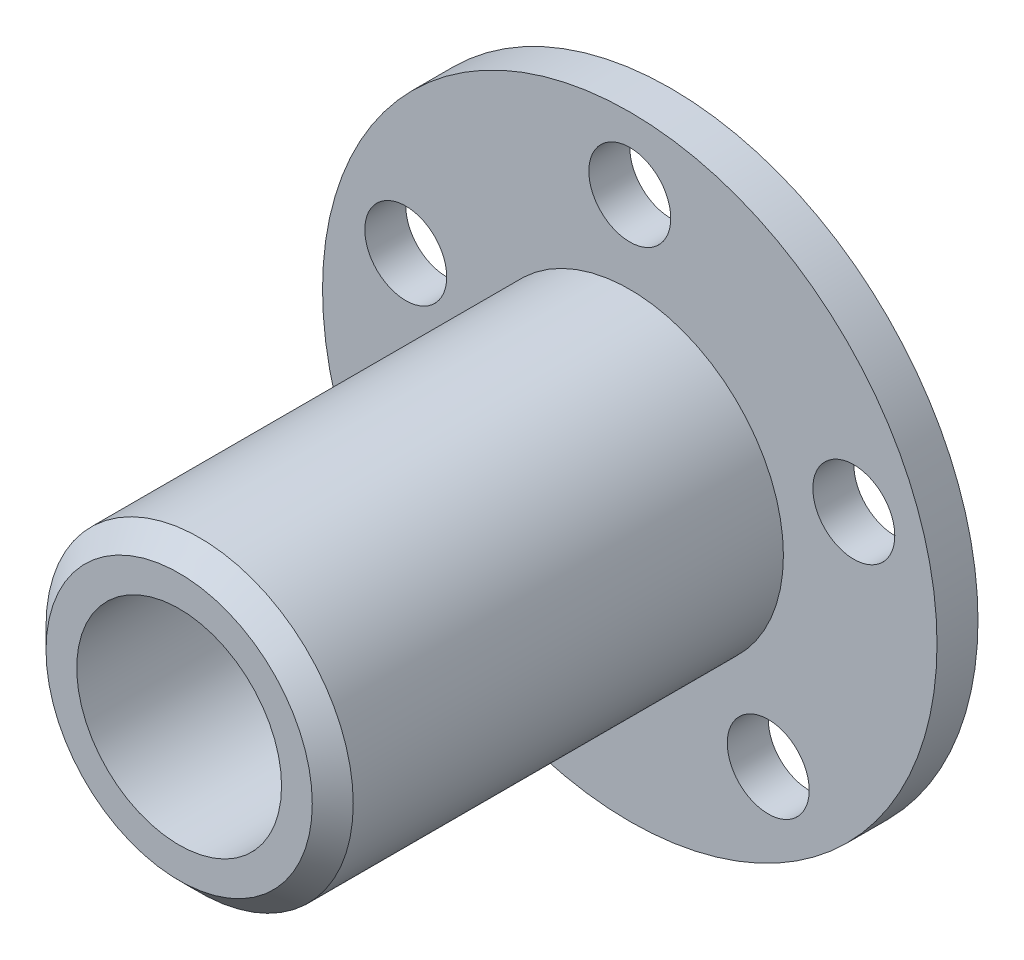
SolidWorks part; units mm, degrees
ref_plane "Front Plane" through (0, 0, 0) normal (0, 0, 1) x (1, 0, 0)
ref_plane "Top Plane" through (0, 0, 0) normal (0, 1, 0) x (1, 0, 0)
ref_plane "Right Plane" through (0, 0, 0) normal (1, 0, 0) x (0, 0, -1)
sketch "Sketch1" plane through (0, 0, 0) normal (0, 0, 1) x (1, 0, 0)
  circle A0 centre (0, 0) radius 15
  dimension "D1" = 30
extrude "Boss-Extrude1" add sketch "Sketch1" along normal blind 2
sketch "Sketch2" plane through (0, 0, 2) normal (0, 0, 1) x (1, 0, 0)
  circle A0 centre (0, 0) radius 7.5
  dimension "D1" = 15
extrude "Boss-Extrude2" add sketch "Sketch2" along normal blind 22
sketch "Sketch3" plane through (0, 0, 24) normal (0, 0, 1) x (1, 0, 0)
  circle A0 centre (0, 0) radius 5
  dimension "D1" = 10
extrude "Cut-Extrude1" cut sketch "Sketch3" against normal through all
sketch "Sketch4" plane through (0, 0, 2) normal (0, 0, 1) x (1, 0, 0)
  circle A0 centre (0, 0) radius 11.5
  circle A1 centre (0, 11.5) radius 2
  circle A2 centre (10.9371, 3.5537) radius 2
  circle A3 centre (6.7595, -9.3037) radius 2
  circle A4 centre (-6.7595, -9.3037) radius 2
  circle A5 centre (-10.9371, 3.5537) radius 2
  point P16 (0, 0)
  dimension "D1" = 23
  dimension "D2" = 4
  dimension "D3" = 5
extrude "Cut-Extrude2" cut sketch "Sketch4" against normal through all contours A1 | A5 | A2 | A3 | A4
chamfer "Chamfer1" distance 1 angle 45 1 edges at (5, 0, 0)
chamfer "Chamfer2" distance 1 angle 45 1 edges at (7.5, 0, 24)
